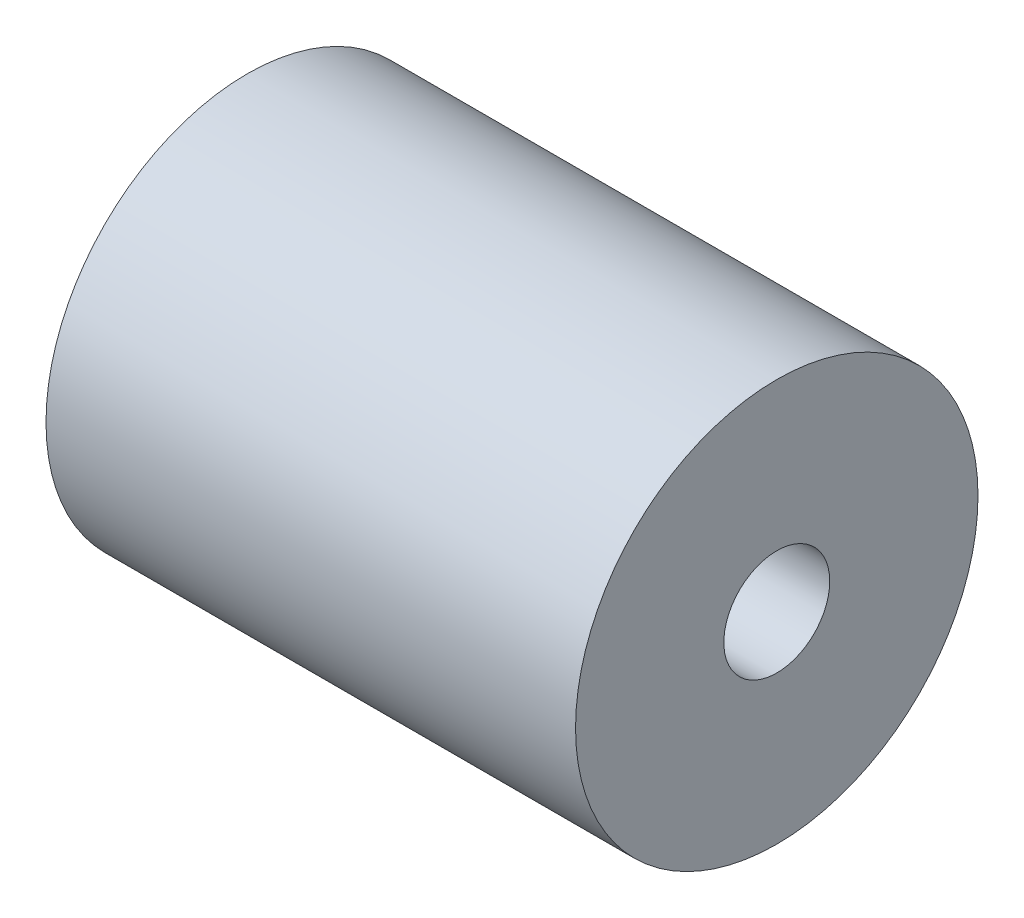
SolidWorks part; units mm, degrees
ref_plane "Front Plane" through (0, 0, 0) normal (0, 0, 1) x (1, 0, 0)
ref_plane "Top Plane" through (0, 0, 0) normal (0, 1, 0) x (1, 0, 0)
ref_plane "Right Plane" through (0, 0, 0) normal (1, 0, 0) x (0, 0, -1)
sketch "Sketch1" plane through (0, 0, 0) normal (1, 0, 0) x (0, 0, -1)
  circle A0 centre (0, 0) radius 9.5
  dimension "D1" = 19
extrude "Boss-Extrude1" add sketch "Sketch1" along normal blind 25
sketch "Sketch2" plane through (25, 0, 0) normal (1, 0, 0) x (0, 0, -1)
  circle A0 centre (0, 0) radius 2.5
  dimension "D1" = 5
extrude "Cut-Extrude1" cut sketch "Sketch2" against normal blind 12.5
sketch "Sketch3" plane through (0, 0, 0) normal (-1, 0, 0) x (0, 0, 1)
  circle A0 centre (0, 0) radius 4
  dimension "D1" = 8
extrude "Cut-Extrude2" cut sketch "Sketch3" against normal blind 12.5
